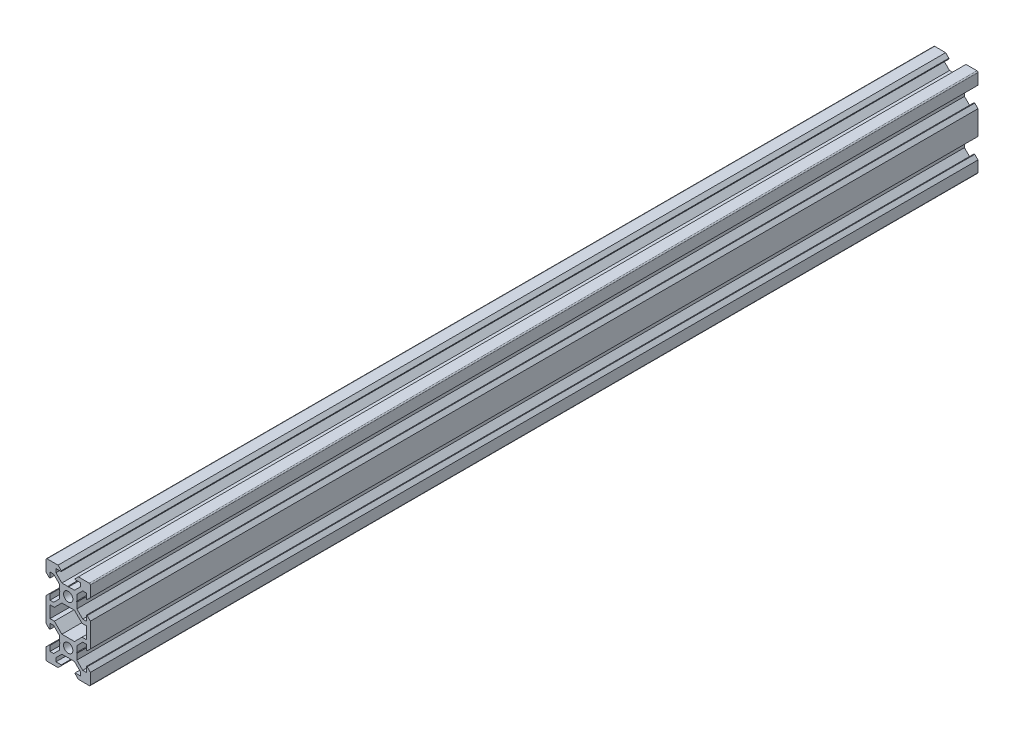
SolidWorks part; units mm, degrees
material "6061-T6 (SS)"
ref_plane "幹" through (0, 0, 0) normal (0, 0, 1) x (1, 0, 0)
ref_plane "你" through (0, 0, 0) normal (0, 1, 0) x (1, 0, 0)
ref_plane "娘" through (0, 0, 0) normal (1, 0, 0) x (0, 0, -1)
sketch "Sketch1" plane through (0, 0, 0) normal (0, 0, 1) x (1, 0, 0)
  line L0 (0, 0) -> (10, 0) construction
  line L1 (9.5, -20) -> (-9.5, -20)
  line L2 (10, -19.5) -> (10, 19.5)
  line L3 (9.5, 20) -> (-9.5, 20)
  line L4 (-10, -19.5) -> (-10, 19.5)
  line L5 (10, -20) -> (-10, 20) construction
  line L6 (10, 20) -> (-10, -20) construction
  circle A0 centre (0, 10) radius 2.1
  circle A1 centre (0, -10) radius 2.1
  arc A2 (-9.5, -20) -> (-10, -19.5) centre (-9.5, -19.5) cw
  arc A3 (9.5, -20) -> (10, -19.5) centre (9.5, -19.5) ccw
  arc A4 (10, 19.5) -> (9.5, 20) centre (9.5, 19.5) ccw
  arc A5 (-9.5, 20) -> (-10, 19.5) centre (-9.5, 19.5) ccw
  point P0 (0, 0)
  line B0 (0, 10) -> (0, 20) construction
  line B1 (0, 13.69) -> (-0.21, 13.9)
  line B2 (-0.21, 13.9) -> (-2.8393, 13.9)
  line B3 (-2.8393, 13.9) -> (-5.5, 16.5607)
  line B4 (-5.5, 16.5607) -> (-5.5, 18.2)
  line B5 (-5.5, 18.2) -> (-3.125, 18.2)
  line B6 (-3.125, 18.2) -> (-3.125, 18.545)
  line B7 (-3.125, 18.545) -> (-4.58, 20)
  line B8 (-4.58, 20) -> (4.58, 20)
  line B9 (0, 10) -> (-5.9132, 15.9132) construction
  line B10 (3.125, 18.545) -> (4.58, 20)
  line B11 (3.125, 18.2) -> (3.125, 18.545)
  line B12 (5.5, 18.2) -> (3.125, 18.2)
  line B13 (5.5, 16.5607) -> (5.5, 18.2)
  line B14 (2.8393, 13.9) -> (5.5, 16.5607)
  line B15 (0.21, 13.9) -> (2.8393, 13.9)
  line B16 (0, 13.69) -> (0.21, 13.9)
  line B17 (0, 10) -> (-10, 10) construction
  line B18 (-3.69, 10) -> (-3.9, 9.79)
  line B19 (-3.9, 9.79) -> (-3.9, 7.1607)
  line B20 (-3.9, 7.1607) -> (-6.5607, 4.5)
  line B21 (-6.5607, 4.5) -> (-8.2, 4.5)
  line B22 (-8.2, 4.5) -> (-8.2, 6.875)
  line B23 (-8.2, 6.875) -> (-8.545, 6.875)
  line B24 (-8.545, 6.875) -> (-10, 5.42)
  line B25 (-10, 5.42) -> (-10, 14.58)
  line B26 (0, 10) -> (-5.9132, 4.0868) construction
  line B27 (-8.545, 13.125) -> (-10, 14.58)
  line B28 (-8.2, 13.125) -> (-8.545, 13.125)
  line B29 (-8.2, 15.5) -> (-8.2, 13.125)
  line B30 (-6.5607, 15.5) -> (-8.2, 15.5)
  line B31 (-3.9, 12.8393) -> (-6.5607, 15.5)
  line B32 (-3.9, 10.21) -> (-3.9, 12.8393)
  line B33 (-3.69, 10) -> (-3.9, 10.21)
  line B34 (0, -10) -> (-10, -10) construction
  line B35 (-3.69, -10) -> (-3.9, -10.21)
  line B36 (-3.9, -10.21) -> (-3.9, -12.8393)
  line B37 (-3.9, -12.8393) -> (-6.5607, -15.5)
  line B38 (-6.5607, -15.5) -> (-8.2, -15.5)
  line B39 (-8.2, -15.5) -> (-8.2, -13.125)
  line B40 (-8.2, -13.125) -> (-8.545, -13.125)
  line B41 (-8.545, -13.125) -> (-10, -14.58)
  line B42 (-10, -14.58) -> (-10, -5.42)
  line B43 (0, -10) -> (-5.9132, -15.9132) construction
  line B44 (-8.545, -6.875) -> (-10, -5.42)
  line B45 (-8.2, -6.875) -> (-8.545, -6.875)
  line B46 (-8.2, -4.5) -> (-8.2, -6.875)
  line B47 (-6.5607, -4.5) -> (-8.2, -4.5)
  line B48 (-3.9, -7.1607) -> (-6.5607, -4.5)
  line B49 (-3.9, -9.79) -> (-3.9, -7.1607)
  line B50 (-3.69, -10) -> (-3.9, -9.79)
  line B51 (0, -10) -> (0, -20) construction
  line B52 (0, -13.69) -> (0.21, -13.9)
  line B53 (0.21, -13.9) -> (2.8393, -13.9)
  line B54 (2.8393, -13.9) -> (5.5, -16.5607)
  line B55 (5.5, -16.5607) -> (5.5, -18.2)
  line B56 (5.5, -18.2) -> (3.125, -18.2)
  line B57 (3.125, -18.2) -> (3.125, -18.545)
  line B58 (3.125, -18.545) -> (4.58, -20)
  line B59 (4.58, -20) -> (-4.58, -20)
  line B60 (0, -10) -> (5.9132, -15.9132) construction
  line B61 (-3.125, -18.545) -> (-4.58, -20)
  line B62 (-3.125, -18.2) -> (-3.125, -18.545)
  line B63 (-5.5, -18.2) -> (-3.125, -18.2)
  line B64 (-5.5, -16.5607) -> (-5.5, -18.2)
  line B65 (-2.8393, -13.9) -> (-5.5, -16.5607)
  line B66 (-0.21, -13.9) -> (-2.8393, -13.9)
  line B67 (0, -13.69) -> (-0.21, -13.9)
  line B68 (0, -10) -> (10, -10) construction
  line B69 (3.69, -10) -> (3.9, -9.79)
  line B70 (3.9, -9.79) -> (3.9, -7.1607)
  line B71 (3.9, -7.1607) -> (6.5607, -4.5)
  line B72 (6.5607, -4.5) -> (8.2, -4.5)
  line B73 (8.2, -4.5) -> (8.2, -6.875)
  line B74 (8.2, -6.875) -> (8.545, -6.875)
  line B75 (8.545, -6.875) -> (10, -5.42)
  line B76 (10, -5.42) -> (10, -14.58)
  line B77 (0, -10) -> (5.9132, -4.0868) construction
  line B78 (8.545, -13.125) -> (10, -14.58)
  line B79 (8.2, -13.125) -> (8.545, -13.125)
  line B80 (8.2, -15.5) -> (8.2, -13.125)
  line B81 (6.5607, -15.5) -> (8.2, -15.5)
  line B82 (3.9, -12.8393) -> (6.5607, -15.5)
  line B83 (3.9, -10.21) -> (3.9, -12.8393)
  line B84 (3.69, -10) -> (3.9, -10.21)
  line B85 (0, 10) -> (10, 10) construction
  line B86 (3.69, 10) -> (3.9, 10.21)
  line B87 (3.9, 10.21) -> (3.9, 12.8393)
  line B88 (3.9, 12.8393) -> (6.5607, 15.5)
  line B89 (6.5607, 15.5) -> (8.2, 15.5)
  line B90 (8.2, 15.5) -> (8.2, 13.125)
  line B91 (8.2, 13.125) -> (8.545, 13.125)
  line B92 (8.545, 13.125) -> (10, 14.58)
  line B93 (10, 14.58) -> (10, 5.42)
  line B94 (0, 10) -> (5.9132, 15.9132) construction
  line B95 (8.545, 6.875) -> (10, 5.42)
  line B96 (8.2, 6.875) -> (8.545, 6.875)
  line B97 (8.2, 4.5) -> (8.2, 6.875)
  line B98 (6.5607, 4.5) -> (8.2, 4.5)
  line B99 (3.9, 7.1607) -> (6.5607, 4.5)
  line B100 (3.9, 9.79) -> (3.9, 7.1607)
  line B101 (3.69, 10) -> (3.9, 9.79)
  line B102 (-8.2, -2.7) -> (-8.2, 2.7)
  line B103 (-8.2, 2.7) -> (-6.2393, 2.7)
  line B104 (-6.2393, 2.7) -> (-2.8393, 6.1)
  line B105 (-2.8393, 6.1) -> (2.8393, 6.1)
  line B106 (0, 6.1) -> (0, 0) construction
  line B107 (0, 0) -> (-8.2, 0) construction
  line B108 (6.2393, 2.7) -> (2.8393, 6.1)
  line B109 (8.2, 2.7) -> (6.2393, 2.7)
  line B110 (8.2, -2.7) -> (8.2, 2.7)
  line B111 (8.2, -2.7) -> (6.2393, -2.7)
  line B112 (6.2393, -2.7) -> (2.8393, -6.1)
  line B113 (-2.8393, -6.1) -> (2.8393, -6.1)
  line B114 (-6.2393, -2.7) -> (-2.8393, -6.1)
  line B115 (-8.2, -2.7) -> (-6.2393, -2.7)
  line B116 (0, 6.1) -> (0, 10) construction
  line B117 (0, 10) -> (-5.0927, 4.9073) construction
  dimension "D4" = 4.2
  dimension "D5" = 0.5
  dimension "D1" = 20
  dimension "D2" = 40
  dimension "D3" = 20
sketch_block_instance "V Slot 1-4"
sketch_block "V Slot 1" parameters "D1"=10, "D2"=11, "D3"=4.3, "D4"=1.8, "D5"=0.21, "D6"=45, "D7"=9.16, "D8"=1.5, "D9"=6.25
sketch_block_instance "V Slot 1-5"
sketch_block_instance "V Slot 1-6"
sketch_block_instance "V Slot 1-7"
sketch_block_instance "V Slot 1-8"
sketch_block_instance "V Slot 1-9"
sketch_block_instance "Center Cutout 1-1"
sketch_block "Center Cutout 1" parameters "D1"=5.4, "D2"=12.2, "D3"=8.2, "D4"=45, "D5"=10, "D6"=1.5
extrude "掰" add sketch "Sketch1" along normal blind 400 contours B101 B86 B87 B88 B89 B90 B91 B92 L2 A4 L3 B10 B11 B12 B13 B14 B15 B16 B1 B2 B3 B4 B5 B6 B7 A5 L4 B27 B28 B29 B30 B31 B32 B33 B18 B19 B20 B21 B22 B23 B24 B44 B45 B46 B47 B48 B49 B50 B35
